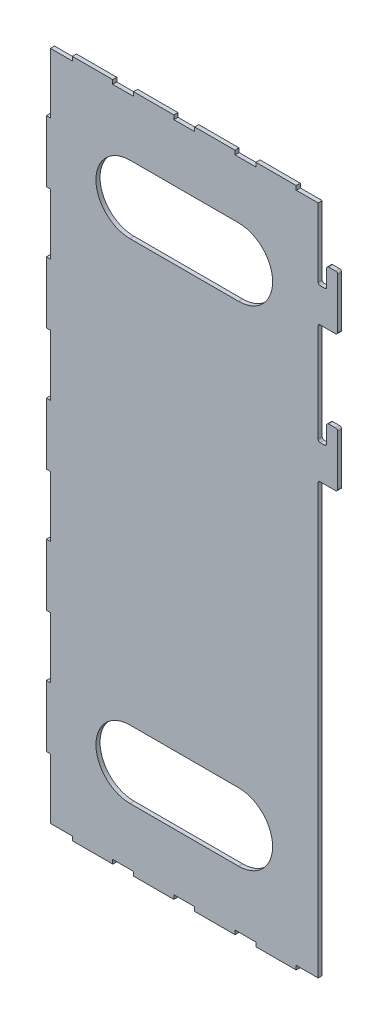
SolidWorks part; units mm, degrees
ref_plane "Alzado" through (0, 0, 0) normal (0, 0, 1) x (1, 0, 0)
ref_plane "Planta" through (0, 0, 0) normal (0, 1, 0) x (1, 0, 0)
ref_plane "Vista lateral" through (0, 0, 0) normal (1, 0, 0) x (0, 0, -1)
sketch "Croquis1" plane through (0, 0, 0) normal (0, 0, 1) x (1, 0, 0)
  line L0 (101.5, 195) -> (104.8, 195)
  line L1 (-100, 250) -> (100, 250)
  line L2 (-100, 250) -> (-100, -250)
  line L3 (-100, -250) -> (100, -250)
  line L4 (100, 250) -> (100, 196.5)
  line L5 (-100, 250) -> (100, -250) construction
  line L6 (-100, -250) -> (100, 250) construction
  line L7 (106.3, 196.5) -> (106.3, 208.5)
  line L8 (107.8, 210) -> (112.8, 210)
  line L9 (114.3, 208.5) -> (114.3, 171.5)
  line L10 (112.8, 170) -> (101.5, 170)
  line L11 (100, 168.5) -> (100, 96.5)
  line L12 (101.5, 95) -> (104.8, 95)
  line L13 (112.8, 70) -> (101.5, 70)
  line L14 (114.3, 108.5) -> (114.3, 71.5)
  line L15 (106.3, 96.5) -> (106.3, 108.5)
  line L16 (107.8, 110) -> (112.8, 110)
  line L22 (100, 68.5) -> (100, -35.6199)
  line L23 (100, -35.6199) -> (100, -250)
  line L24 (114.3, -30) -> (100, -30) [skipped]
  line L25 (114.3, 10) -> (114.3, -30) [skipped]
  line L26 (106.3, 10) -> (114.3, 10) [skipped]
  line L27 (106.3, -5) -> (106.3, 10) [skipped]
  line L28 (100, -5) -> (106.3, -5) [skipped]
  arc A0 (114.3, 171.5) -> (112.8, 170) centre (112.8, 171.5) cw
  arc A1 (112.8, 210) -> (114.3, 208.5) centre (112.8, 208.5) cw
  arc A2 (106.3, 208.5) -> (107.8, 210) centre (107.8, 208.5) cw
  arc A3 (104.8, 195) -> (106.3, 196.5) centre (104.8, 196.5) ccw
  arc A4 (101.5, 195) -> (100, 196.5) centre (101.5, 196.5) cw
  arc A5 (101.5, 170) -> (100, 168.5) centre (101.5, 168.5) ccw
  arc A6 (101.5, 70) -> (100, 68.5) centre (101.5, 68.5) ccw
  arc A7 (112.8, 70) -> (114.3, 71.5) centre (112.8, 71.5) ccw
  arc A8 (114.3, 108.5) -> (112.8, 110) centre (112.8, 108.5) ccw
  arc A9 (106.3, 108.5) -> (107.8, 110) centre (107.8, 108.5) cw
  arc A10 (104.8, 95) -> (106.3, 96.5) centre (104.8, 96.5) ccw
  arc A11 (101.5, 95) -> (100, 96.5) centre (101.5, 96.5) cw
  point P0 (0, 0)
  point P8 (100, -32.2932)
  point P13 (0, 0)
  point P21 (100, -35.6199)
  point P22 (100, -44.0886)
  point P23 (100, -36.4173)
  point P46 (100, 170)
  dimension "D10" = 1.5
  dimension "D11" = 1.5
  dimension "D12" = 1.5
  dimension "D1" = 500
  dimension "D2" = 200
  dimension "D3" = 6.3
  dimension "D4" = 8
  dimension "D5" = 40
  dimension "D6" = 40
  dimension "D7" = 25
  dimension "D9" = 60
  dimension "D8" = 3
extrude "Saliente-Extruir1" add sketch "Croquis1" along normal blind 3
sketch "Croquis2" plane through (0, 0, 3) normal (0, 0, 1) x (1, 0, 0)
  line L0 (100, 250) -> (100, 247)
  line L1 (100, -250) -> (100, -247)
  line L2 (41.5, 205) -> (-38.5, 205)
  line L3 (-38.5, 155) -> (41.5, 155)
  line L4 (41.5, 205) -> (-38.5, 205)
  line L5 (-38.5, 155) -> (41.5, 155)
  line L6 (-38.5, -205) -> (41.5, -205)
  line L7 (41.5, -155) -> (-38.5, -155)
  line L8 (-38.5, -205) -> (41.5, -205)
  line L9 (41.5, -155) -> (-38.5, -155)
  line L12 (-100, 250) -> (100, 250) construction
  line L14 (-100, 250) -> (-100, -250) construction
  line L17 (-100, -250) -> (100, -250)
  line L18 (-100, 250) -> (-100, -250)
  line L19 (100, 250) -> (-100, 250)
  line L64 (-6.15, -247) -> (9.15, -247)
  line L65 (9.15, -247) -> (9.15, -250)
  line L66 (9.15, -250) -> (38.85, -250)
  line L67 (38.85, -250) -> (38.85, -247)
  line L68 (38.85, -247) -> (54.15, -247)
  line L69 (54.15, -247) -> (54.15, -250)
  line L70 (54.15, -250) -> (83.85, -250)
  line L71 (83.85, -250) -> (83.85, -247)
  line L72 (83.85, -247) -> (100, -247)
  line L73 (100, -247) -> (100, 247)
  line L74 (100, 247) -> (83.85, 247)
  line L75 (83.85, 247) -> (83.85, 253)
  line L76 (83.85, 253) -> (54.15, 253)
  line L77 (54.15, 253) -> (54.15, 247)
  line L78 (54.15, 247) -> (38.85, 247)
  line L79 (38.85, 247) -> (38.85, 253)
  line L80 (38.85, 253) -> (9.15, 253)
  line L81 (9.15, 253) -> (9.15, 247)
  line L82 (9.15, 247) -> (-6.15, 247)
  line L83 (-6.15, 247) -> (-6.15, 253)
  line L84 (-6.15, 253) -> (-35.85, 253)
  line L85 (-35.85, 253) -> (-35.85, 247)
  line L86 (-35.85, 247) -> (-51.15, 247)
  line L87 (-51.15, 247) -> (-51.15, 253)
  line L88 (-51.15, 253) -> (-80.85, 253)
  line L89 (-80.85, 253) -> (-80.85, 247)
  line L90 (-80.85, 247) -> (-97, 247)
  line L91 (-97, 247) -> (-97, 202.65)
  line L92 (-97, 202.65) -> (-100, 202.65)
  line L93 (-100, 202.65) -> (-100, 157.35)
  line L94 (-100, 157.35) -> (-97, 157.35)
  line L95 (-97, 157.35) -> (-97, 112.65)
  line L96 (-97, 112.65) -> (-100, 112.65)
  line L97 (-100, 112.65) -> (-100, 67.35)
  line L98 (-100, 67.35) -> (-97, 67.35)
  line L99 (-97, 67.35) -> (-97, 22.65)
  line L100 (-97, 22.65) -> (-100, 22.65)
  line L101 (-100, 22.65) -> (-100, -22.65)
  line L102 (-100, -22.65) -> (-97, -22.65)
  line L103 (-97, -22.65) -> (-97, -67.35)
  line L104 (-97, -67.35) -> (-100, -67.35)
  line L105 (-100, -67.35) -> (-100, -112.65)
  line L106 (-100, -112.65) -> (-97, -112.65)
  line L107 (-97, -112.65) -> (-97, -157.35)
  line L108 (-97, -157.35) -> (-100, -157.35)
  line L109 (-100, -157.35) -> (-100, -202.65)
  line L110 (-100, -202.65) -> (-97, -202.65)
  line L111 (-97, -202.65) -> (-97, -247)
  line L112 (-97, -247) -> (-80.85, -247)
  line L113 (-80.85, -247) -> (-80.85, -250)
  line L114 (-80.85, -250) -> (-51.15, -250)
  line L115 (-51.15, -250) -> (-51.15, -247)
  line L116 (-51.15, -247) -> (-35.85, -247)
  line L117 (-35.85, -247) -> (-35.85, -250)
  line L118 (-35.85, -250) -> (-6.15, -250)
  line L119 (-6.15, -250) -> (-6.15, -247)
  line L120 (-6.15, -247) -> (9.15, -247)
  line L121 (9.15, -247) -> (9.15, -250)
  line L122 (9.15, -250) -> (38.85, -250)
  line L123 (38.85, -250) -> (38.85, -247)
  line L124 (38.85, -247) -> (54.15, -247)
  line L125 (54.15, -247) -> (54.15, -250)
  line L126 (54.15, -250) -> (83.85, -250)
  line L127 (83.85, -250) -> (83.85, -247)
  line L128 (83.85, -247) -> (100, -247)
  line L130 (100, 247) -> (83.85, 247)
  line L131 (83.85, 247) -> (83.85, 253)
  line L132 (83.85, 253) -> (54.15, 253)
  line L133 (54.15, 253) -> (54.15, 247)
  line L134 (54.15, 247) -> (38.85, 247)
  line L135 (38.85, 247) -> (38.85, 253)
  line L136 (38.85, 253) -> (9.15, 253)
  line L137 (9.15, 253) -> (9.15, 247)
  line L138 (9.15, 247) -> (-6.15, 247)
  line L139 (-6.15, 247) -> (-6.15, 253)
  line L140 (-6.15, 253) -> (-35.85, 253)
  line L141 (-35.85, 253) -> (-35.85, 247)
  line L142 (-35.85, 247) -> (-51.15, 247)
  line L143 (-51.15, 247) -> (-51.15, 253)
  line L144 (-51.15, 253) -> (-80.85, 253)
  line L145 (-80.85, 253) -> (-80.85, 247)
  line L146 (-80.85, 247) -> (-97, 247)
  line L147 (-97, 247) -> (-97, 202.65)
  line L148 (-97, 202.65) -> (-100, 202.65)
  line L149 (-100, 202.65) -> (-100, 157.35)
  line L150 (-100, 157.35) -> (-97, 157.35)
  line L151 (-97, 157.35) -> (-97, 112.65)
  line L152 (-97, 112.65) -> (-100, 112.65)
  line L153 (-100, 112.65) -> (-100, 67.35)
  line L154 (-100, 67.35) -> (-97, 67.35)
  line L155 (-97, 67.35) -> (-97, 22.65)
  line L156 (-97, 22.65) -> (-100, 22.65)
  line L157 (-100, 22.65) -> (-100, -22.65)
  line L158 (-100, -22.65) -> (-97, -22.65)
  line L159 (-97, -22.65) -> (-97, -67.35)
  line L160 (-97, -67.35) -> (-100, -67.35)
  line L161 (-100, -67.35) -> (-100, -112.65)
  line L162 (-100, -112.65) -> (-97, -112.65)
  line L163 (-97, -112.65) -> (-97, -157.35)
  line L164 (-97, -157.35) -> (-100, -157.35)
  line L165 (-100, -157.35) -> (-100, -202.65)
  line L166 (-100, -202.65) -> (-97, -202.65)
  line L167 (-97, -202.65) -> (-97, -247)
  line L168 (-97, -247) -> (-80.85, -247)
  line L169 (-80.85, -247) -> (-80.85, -250)
  line L170 (-80.85, -250) -> (-51.15, -250)
  line L171 (-51.15, -250) -> (-51.15, -247)
  line L172 (-51.15, -247) -> (-35.85, -247)
  line L173 (-35.85, -247) -> (-35.85, -250)
  line L174 (-35.85, -250) -> (-6.15, -250)
  line L175 (-6.15, -250) -> (-6.15, -247)
  line L826 (-100, -250) -> (100, -250) construction
  line L2568 (100, 247) -> (100, -247)
  arc A3 (-38.5, 205) -> (-38.5, 155) centre (-38.5, 180) ccw
  arc A4 (41.5, 155) -> (66.5, 180) centre (41.5, 180) ccw
  arc A5 (66.5, 180) -> (41.5, 205) centre (41.5, 180) ccw
  arc A6 (-38.5, 205) -> (-38.5, 155) centre (-38.5, 180) ccw
  arc A7 (41.5, 155) -> (66.5, 180) centre (41.5, 180) ccw
  arc A8 (66.5, 180) -> (41.5, 205) centre (41.5, 180) ccw
  arc A9 (41.5, -205) -> (66.5, -180) centre (41.5, -180) ccw
  arc A10 (-38.5, -155) -> (-38.5, -205) centre (-38.5, -180) ccw
  arc A11 (66.5, -180) -> (41.5, -155) centre (41.5, -180) ccw
  arc A12 (41.5, -205) -> (66.5, -180) centre (41.5, -180) ccw
  arc A13 (-38.5, -155) -> (-38.5, -205) centre (-38.5, -180) ccw
  arc A14 (66.5, -180) -> (41.5, -155) centre (41.5, -180) ccw
  dimension "D1" = 0
  dimension "D2" = 0
  dimension "D3" = 0
extrude "Cortar-Extruir1" cut sketch "Croquis2" against normal up to next
